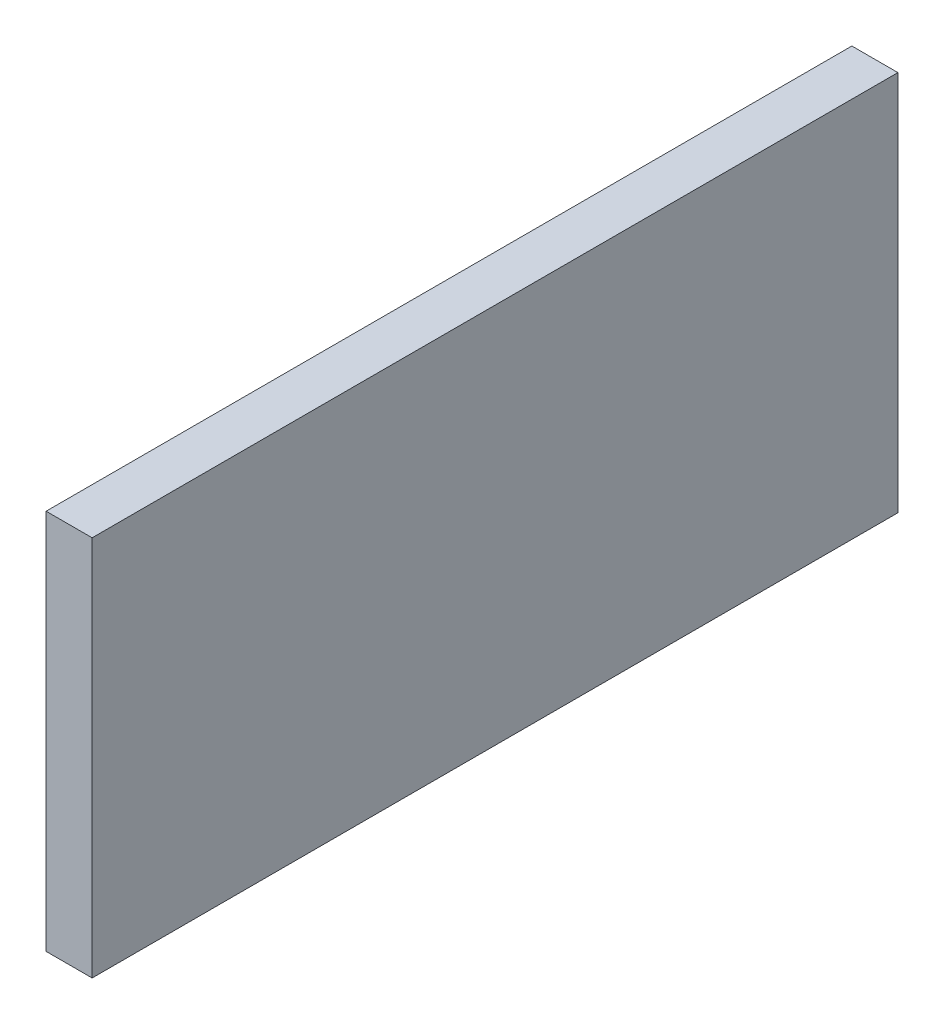
SolidWorks part; units mm, degrees
ref_plane "Front Plane" through (0, 0, 0) normal (0, 0, 1) x (1, 0, 0)
ref_plane "Top Plane" through (0, 0, 0) normal (0, 1, 0) x (1, 0, 0)
ref_plane "Right Plane" through (0, 0, 0) normal (1, 0, 0) x (0, 0, -1)
sketch "Sketch1" plane through (0, 0, 0) normal (0, 1, 0) x (1, 0, 0)
  line L1 (0, 0) -> (2.54, 0)
  line L2 (0, 0) -> (0, 44.45)
  line L3 (0, 44.45) -> (2.54, 44.45)
  line L4 (2.54, 0) -> (2.54, 44.45)
  dimension "D1" = 2.54
  dimension "D2" = 44.45
extrude "Boss-Extrude1" add sketch "Sketch1" along normal blind 21.0312
